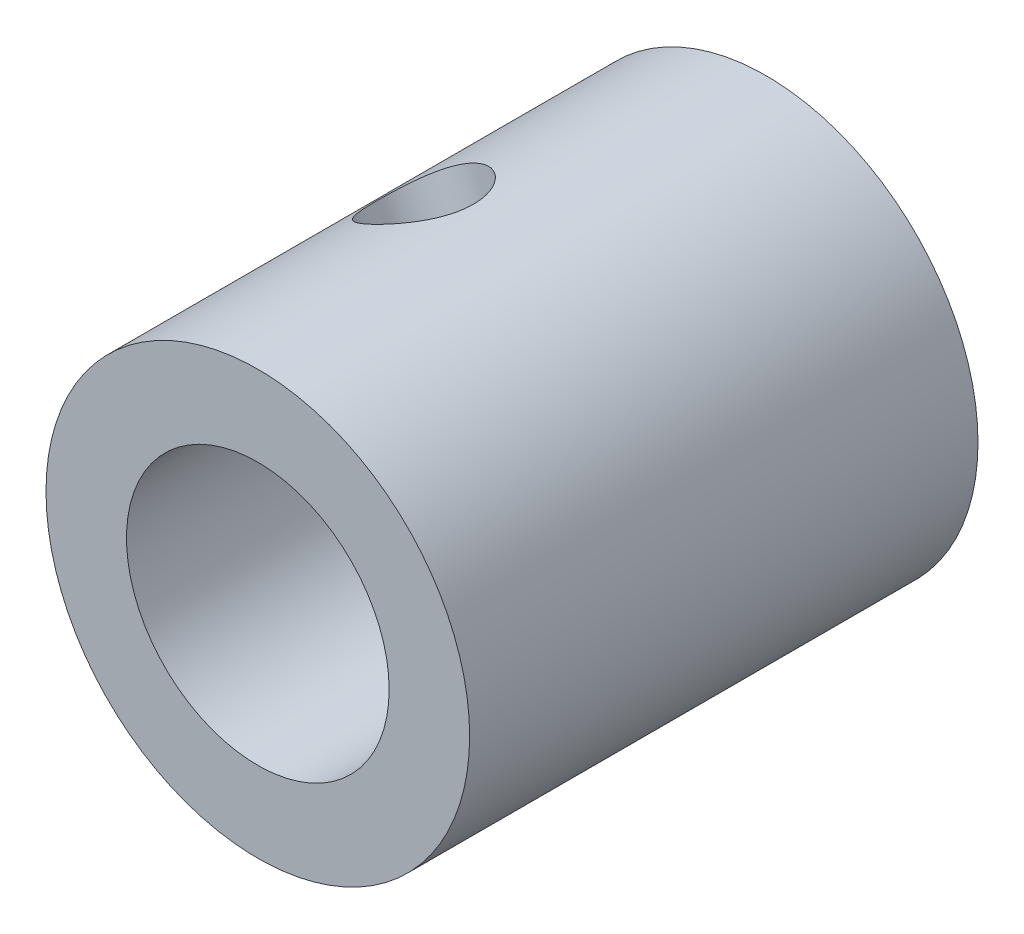
SolidWorks part; units mm, degrees
ref_plane "正面" through (0, 0, 0) normal (0, 0, 1) x (1, 0, 0)
ref_plane "平面" through (0, 0, 0) normal (0, 1, 0) x (1, 0, 0)
ref_plane "右側面" through (0, 0, 0) normal (1, 0, 0) x (0, 0, -1)
sketch "ｽｹｯﾁ1" plane through (0, 0, 0) normal (0, 0, 1) x (1, 0, 0)
  circle A0 centre (0, 0) radius 3.1
  circle A1 centre (0, 0) radius 5
  dimension "D1" = 6.2
  dimension "D2" = 10
extrude "ﾎﾞｽ - 押し出し1" add sketch "ｽｹｯﾁ1" along normal blind 12
sketch3d "3Dｽｹｯﾁ3"
  line L0 (0, 0, 0) -> (0, 0, 5.9997)
  circle A0 centre (0, 0, 5.9997) radius 1.4482
  point P4 (0, 1.4482, 5.9997)
hole_wizard "M3x0.5 ねじ穴1" positions "3Dｽｹｯﾁ5" profile "ｽｹｯﾁ3" tap size "M3x0.5" standard "JIS"
sketch3d "3Dｽｹｯﾁ5"
  point P0 (-2.11, 4.533, 6)
  dimension "D1" = 6
sketch "ｽｹｯﾁ3" plane through (-2.11, 4.533, 6) normal (0, 0, 1) x (-0.9066, -0.422, 0)
  line L0 (0, 0) -> (0, 4.7511)
  line L1 (0, 4.7511) -> (1.25, 4)
  line L2 (1.25, 4) -> (1.25, 0)
  line L5 (1.25, 0) -> (0, 0)
  line L10 (0, 4.7511) -> (-1.25, 4) construction
  line L11 (0, -6.35) -> (0, 107.95) construction
  dimension "ねじ下穴ﾄﾞﾘﾙ直径" = 2.5
  dimension "ねじ下穴ﾄﾞﾘﾙの深さ" = 4
  dimension "ﾄﾞﾘﾙ角度" = 118
cosmetic thread "穴のねじ山1" parameters "D1"=2.1632, "D2"=3
